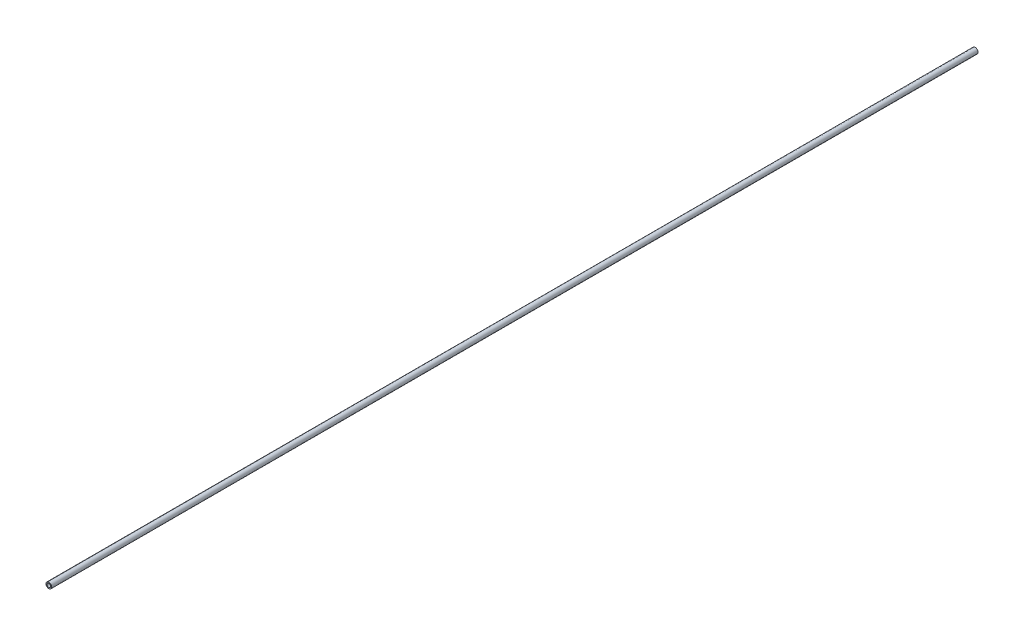
SolidWorks part; units mm, degrees
ref_plane "Front" through (0, 0, 0) normal (0, 0, 1) x (1, 0, 0)
ref_plane "Top" through (0, 0, 0) normal (0, 1, 0) x (1, 0, 0)
ref_plane "Side" through (0, 0, 0) normal (1, 0, 0) x (0, 0, -1)
sketch "PipeSketch" plane through (0, 0, 0) normal (0, 0, 1) x (1, 0, 0)
  circle A0 centre (0, 0) radius 16.764
  circle A1 centre (0, 0) radius 10.414
  dimension "OuterDiameter" = 33.528
  dimension "InnerDiameter" = 20.828
extrude "Extrusion" add sketch "PipeSketch" along normal blind 5486.4
sketch "FilterSketch" plane through (0, 0, 0) normal (0, 0, 1) x (1, 0, 0)
  circle A0 centre (0, 0) radius 12.7 construction
  dimension "NominalDiameter" = 25.4
